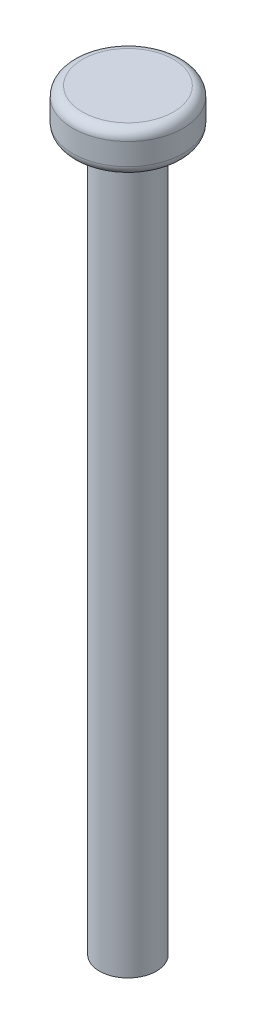
SolidWorks part; units mm, degrees
ref_plane "Спереди" through (0, 0, 0) normal (0, 0, 1) x (1, 0, 0)
ref_plane "Сверху" through (0, 0, 0) normal (0, 1, 0) x (1, 0, 0)
ref_plane "Справа" through (0, 0, 0) normal (1, 0, 0) x (0, 0, -1)
sketch "Sketch1" plane through (0, 0, 0) normal (0, 1, 0) x (1, 0, 0)
  circle A0 centre (0, 0) radius 3
  dimension "D1" = 6
extrude "Boss-Extrude1" add sketch "Sketch1" along normal blind 75
sketch "Sketch2" plane through (0, 75, 0) normal (0, 1, 0) x (1, 0, 0)
  circle A0 centre (0, 0) radius 5.8
  dimension "D1" = 11.6
extrude "Boss-Extrude2" add sketch "Sketch2" along normal blind 4.3
fillet "Fillet1" radius 1 2 edges at (0, 75, 5.8) (0, 79.3, 5.8)
